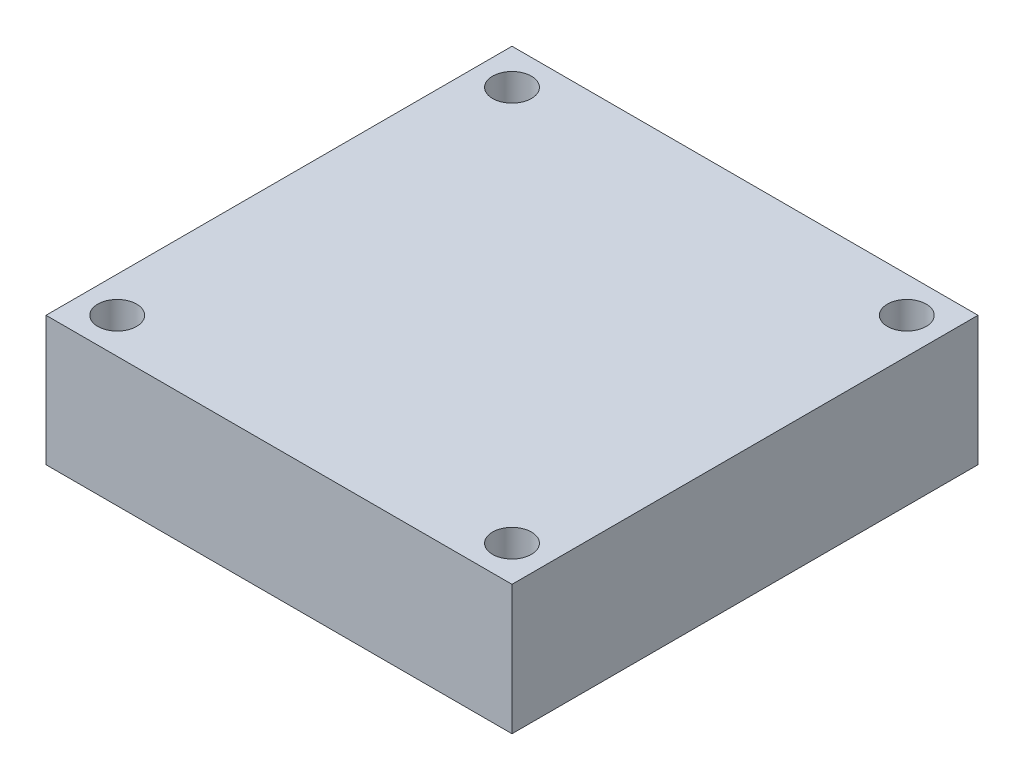
SolidWorks part; units mm, degrees
ref_plane "Front Plane" through (0, 0, 0) normal (0, 0, 1) x (1, 0, 0)
ref_plane "Top Plane" through (0, 0, 0) normal (0, 1, 0) x (1, 0, 0)
ref_plane "Right Plane" through (0, 0, 0) normal (1, 0, 0) x (0, 0, -1)
sketch "Sketch1" plane through (0, 0, 0) normal (0, 1, 0) x (1, 0, 0)
  line L0 (0, 18) -> (0, -18) construction
  line L1 (-18, -18) -> (18, -18)
  line L2 (-18, -18) -> (-18, 18)
  line L3 (-18, 18) -> (18, 18)
  line L4 (18, -18) -> (18, 18)
  line L5 (18, 0) -> (-18, 0) construction
  point P8 (0, 0)
  dimension "D1" = 36
extrude "Boss-Extrude1" add sketch "Sketch1" along normal blind 10
sketch "Sketch2" plane through (0, 10, 0) normal (0, 1, 0) x (1, 0, 0)
  line L0 (0, 18) -> (0, -18) construction
  line L1 (18, 18) -> (-18, 18) construction
  line L2 (-18, -18) -> (18, -18) construction
  line L3 (-18, 0) -> (18, 0) construction
  line L4 (-18, 18) -> (-18, -18) construction
  line L5 (18, -18) -> (18, 18) construction
  line L6 (15.25, 15.25) -> (-15.25, 15.25) construction
  line L7 (-15.25, 15.25) -> (-15.25, -15.25) construction
  line L8 (-15.25, -15.25) -> (15.25, -15.25) construction
  line L9 (15.25, -15.25) -> (15.25, 15.25) construction
  circle A0 centre (-15.25, 15.25) radius 1.5
  circle A1 centre (15.25, 15.25) radius 1.5
  circle A2 centre (15.25, -15.25) radius 1.5
  circle A3 centre (-15.25, -15.25) radius 1.5
  point P20 (0, 15.25)
  point P21 (-15.25, 0)
  dimension "D3" = 3
  dimension "D1" = 30.5
  dimension "D2" = 30.5
extrude "Cut-Extrude1" cut sketch "Sketch2" against normal blind 10
